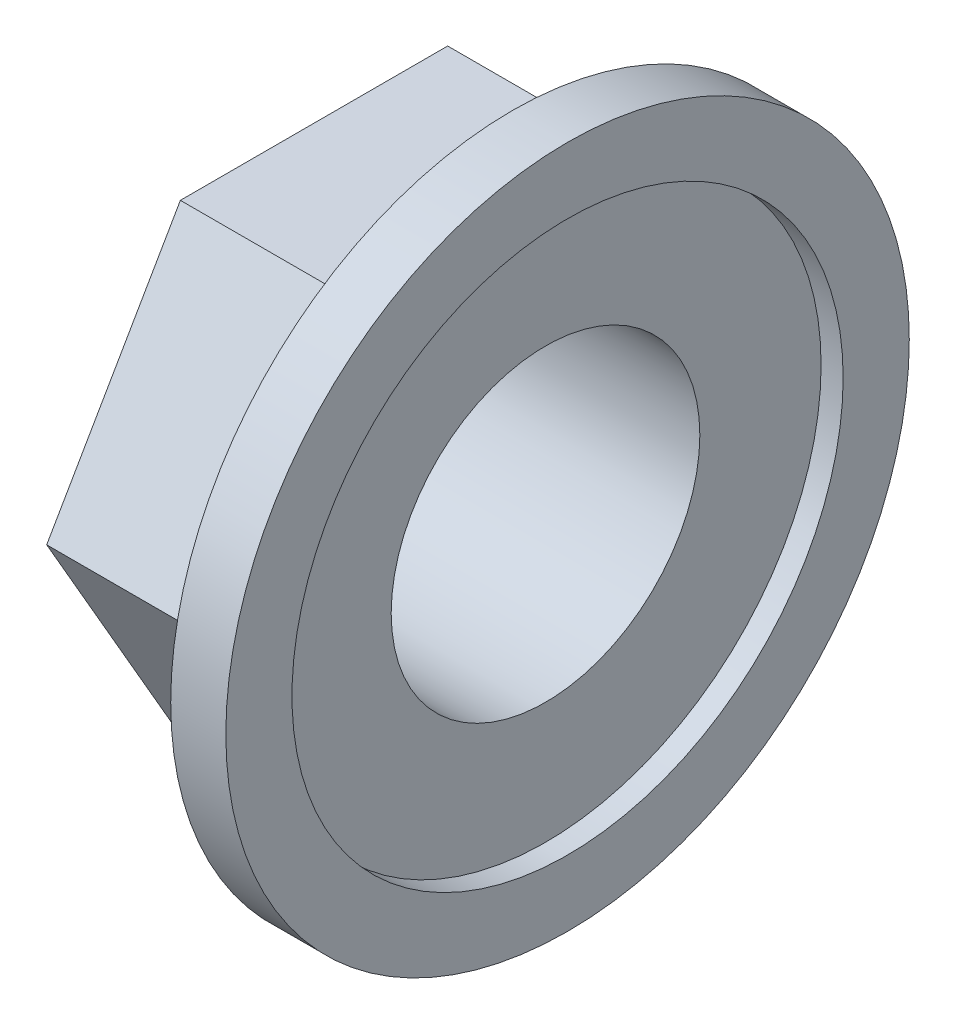
SolidWorks part; units mm, degrees
material "PVC Rigid"
ref_plane "Front Plane" through (0, 0, 0) normal (0, 0, 1) x (1, 0, 0)
ref_plane "Top Plane" through (0, 0, 0) normal (0, 1, 0) x (1, 0, 0)
ref_plane "Right Plane" through (0, 0, 0) normal (1, 0, 0) x (0, 0, -1)
sketch "Sketch1" plane through (0, 0, 0) normal (1, 0, 0) x (0, 0, -1)
  circle A0 centre (0, 0) radius 15.5
  dimension "D1" = 31
extrude "Boss-Extrude2" add sketch "Sketch1" along normal blind 2.5
sketch "Sketch2" plane through (2.5, 0, 0) normal (1, 0, 0) x (0, 0, -1)
  circle A0 centre (0, 0) radius 12.5
  dimension "D1" = 25
extrude "Cut-Extrude1" cut sketch "Sketch2" against normal blind 1
sketch "Sketch3" plane through (0, 0, 0) normal (-1, 0, 0) x (0, 0, 1)
  line L1 (12.1244, 0) -> (6.0622, 10.5)
  line L2 (6.0622, 10.5) -> (-6.0622, 10.5)
  line L3 (-6.0622, 10.5) -> (-12.1244, 0)
  line L4 (-12.1244, 0) -> (-6.0622, -10.5)
  line L5 (-6.0622, -10.5) -> (6.0622, -10.5)
  line L6 (6.0622, -10.5) -> (12.1244, 0)
  circle A0 centre (0, 0) radius 10.5 construction
  dimension "D1" = 21
extrude "Boss-Extrude3" add sketch "Sketch3" along normal blind 9
sketch "Sketch4" plane through (-9, 0, 0) normal (-1, 0, 0) x (0, 0, 1)
  circle A0 centre (0, 0) radius 7
  dimension "D1" = 14
extrude "Cut-Extrude2" cut sketch "Sketch4" against normal through all both and the other way through all
